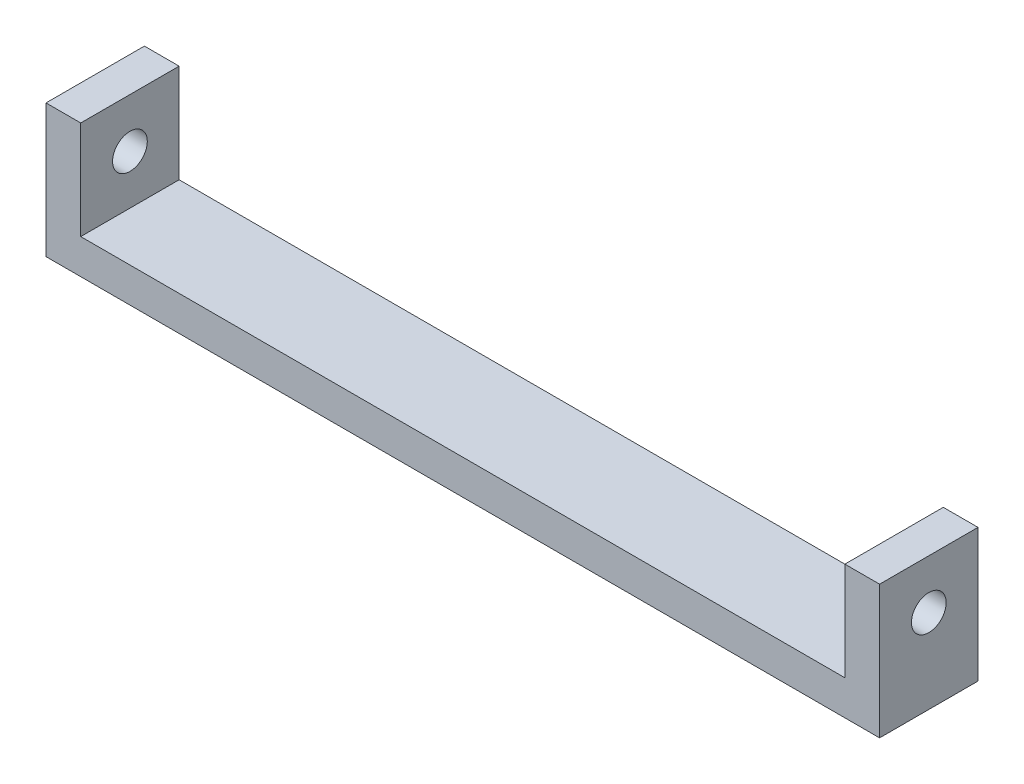
SolidWorks part; units mm, degrees
ref_plane "Front Plane" through (0, 0, 0) normal (0, 0, 1) x (1, 0, 0)
ref_plane "Top Plane" through (0, 0, 0) normal (0, 1, 0) x (1, 0, 0)
ref_plane "Right Plane" through (0, 0, 0) normal (1, 0, 0) x (0, 0, -1)
sketch "Sketch1" plane through (0, 0, 0) normal (1, 0, 0) x (0, 0, -1)
  line L0 (0, 0) -> (1.6017, 0) construction
  line L1 (1.5877, 2.75) -> (-1.5877, 2.75)
  line L2 (-1.5877, 2.75) -> (-3.1754, 0)
  line L3 (-3.1754, 0) -> (-1.5877, -2.75)
  line L4 (-1.5877, -2.75) -> (1.5877, -2.75)
  line L5 (1.5877, -2.75) -> (3.1754, 0)
  line L6 (3.1754, 0) -> (1.5877, 2.75)
  line L8 (-4.25, -4.25) -> (4.25, -4.25)
  line L9 (-4.25, -4.25) -> (-4.25, 4.25)
  line L10 (-4.25, 4.25) -> (4.25, 4.25)
  line L11 (4.25, -4.25) -> (4.25, 4.25)
  line L12 (-4.25, -4.25) -> (4.25, 4.25) construction
  line L13 (-4.25, 4.25) -> (4.25, -4.25) construction
  circle A0 centre (0, 0) radius 2.75 construction
  dimension "D1" = 5.5
  dimension "D2" = 8.5
  dimension "D3" = 8.5
extrude "Boss-Extrude1" add sketch "Sketch1" along normal blind 5
sketch "Sketch2" plane through (0, 0, 0) normal (-1, 0, 0) x (0, 0, 1)
  line L1 (-4.25, -4.25) -> (4.25, -4.25)
  line L2 (-4.25, -4.25) -> (-4.25, 4.25)
  line L3 (-4.25, 4.25) -> (4.25, 4.25)
  line L4 (4.25, -4.25) -> (4.25, 4.25)
  line L5 (-4.25, -4.25) -> (4.25, 4.25) construction
  line L6 (-4.25, 4.25) -> (4.25, -4.25) construction
  point P0 (0, 0)
extrude "Boss-Extrude2" add sketch "Sketch2" along normal blind 2
sketch "Sketch3" plane through (0, 0, 0) normal (1, 0, 0) x (0, 0, -1)
  circle A0 centre (0, 0) radius 1.5
  dimension "D1" = 3
extrude "Cut-Extrude1" cut sketch "Sketch3" against normal blind 2
sketch "Sketch4" plane through (0, -4.25, 0) normal (0, -1, 0) x (1, 0, 0)
  line L0 (5, -4.25) -> (-2, -4.25) construction
  line L1 (-2, 4.25) -> (78, 4.25)
  line L2 (-2, 4.25) -> (-2, -4.25)
  line L3 (-2, -4.25) -> (78, -4.25)
  line L4 (78, 4.25) -> (78, -4.25)
  dimension "D1" = 80
extrude "Boss-Extrude3" add sketch "Sketch4" along normal blind 3
sketch "Sketch5" plane through (0, -4.25, 0) normal (0, 1, 0) x (1, 0, 0)
  line L0 (78, -4.25) -> (5, -4.25) construction
  line L1 (78, 4.25) -> (71, 4.25)
  line L2 (78, 4.25) -> (78, -4.25)
  line L3 (78, -4.25) -> (71, -4.25)
  line L4 (71, 4.25) -> (71, -4.25)
  dimension "D1" = 7
extrude "Boss-Extrude4" add sketch "Sketch5" along normal up to surface (8.5 mm away) up to face at (1.5, 4.25, 0)
sketch "Sketch6" plane through (71, 0, 0) normal (-1, 0, 0) x (0, 0, 1)
  line L0 (-4.25, -4.25) -> (4.25, -4.25) construction
  line L1 (3.1754, 0) -> (1.5877, 2.75)
  line L2 (1.5877, 2.75) -> (-1.5877, 2.75)
  line L3 (-1.5877, 2.75) -> (-3.1754, 0)
  line L4 (-3.1754, 0) -> (-1.5877, -2.75)
  line L5 (-1.5877, -2.75) -> (1.5877, -2.75)
  line L6 (1.5877, -2.75) -> (3.1754, 0)
  circle A0 centre (0, 0) radius 2.75 construction
  dimension "D1" = 5.5
extrude "Cut-Extrude2" cut sketch "Sketch6" against normal blind 5
sketch "Sketch7" plane through (76, 0, 0) normal (-1, 0, 0) x (0, 0, 1)
  circle A0 centre (0, 0) radius 1.5
  dimension "D1" = 3
extrude "Cut-Extrude3" cut sketch "Sketch7" against normal blind 5
sketch "Sketch8" plane through (-2, 0, 0) normal (-1, 0, 0) x (0, 0, 1)
  line L0 (-1.5877, 2.75) -> (1.5877, 2.75) construction
  line L1 (1.5877, 2.75) -> (3.1754, 0) construction
  line L2 (3.1754, 0) -> (1.5877, -2.75) construction
  line L3 (1.5877, -2.75) -> (-1.5877, -2.75) construction
  line L4 (-1.5877, -2.75) -> (-3.1754, 0) construction
  line L5 (-3.1754, 0) -> (-1.5877, 2.75) construction
  line L6 (-1.5877, 2.75) -> (1.5877, 2.75)
  line L7 (1.5877, 2.75) -> (3.1754, 0)
  line L8 (3.1754, 0) -> (1.5877, -2.75)
  line L9 (1.5877, -2.75) -> (-1.5877, -2.75)
  line L10 (-1.5877, -2.75) -> (-3.1754, 0)
  line L11 (-3.1754, 0) -> (-1.5877, 2.75)
extrude "Cut-Extrude4" cut sketch "Sketch8" against normal blind 10
sketch "Sketch9" plane through (5, 0, 0) normal (1, 0, 0) x (0, 0, -1)
  line L1 (-4.25, 4.25) -> (4.25, 4.25)
  line L2 (-4.25, 4.25) -> (-4.25, -4.25)
  line L3 (-4.25, -4.25) -> (4.25, -4.25)
  line L4 (4.25, 4.25) -> (4.25, -4.25)
  circle A0 centre (0, 0) radius 1.5
  dimension "D1" = 3
extrude "Boss-Extrude5" add sketch "Sketch9" against normal blind 2
sketch "Sketch10" plane through (78, 0, 0) normal (1, 0, 0) x (0, 0, -1)
  line L0 (-3.1754, 0) -> (-1.5877, 2.75) construction
  line L1 (-1.5877, -2.75) -> (-3.1754, 0) construction
  line L2 (1.5877, -2.75) -> (-1.5877, -2.75) construction
  line L3 (3.1754, 0) -> (1.5877, -2.75) construction
  line L4 (1.5877, 2.75) -> (3.1754, 0) construction
  line L5 (-1.5877, 2.75) -> (1.5877, 2.75) construction
  line L6 (-3.1754, 0) -> (-1.5877, 2.75)
  line L7 (-1.5877, -2.75) -> (-3.1754, 0)
  line L8 (1.5877, -2.75) -> (-1.5877, -2.75)
  line L9 (3.1754, 0) -> (1.5877, -2.75)
  line L10 (1.5877, 2.75) -> (3.1754, 0)
  line L11 (-1.5877, 2.75) -> (1.5877, 2.75)
extrude "Cut-Extrude5" cut sketch "Sketch10" against normal blind 2
sketch "Sketch11" plane through (71, 0, 0) normal (-1, 0, 0) x (0, 0, 1)
  line L1 (-4.25, 4.25) -> (4.25, 4.25)
  line L2 (-4.25, 4.25) -> (-4.25, -4.25)
  line L3 (-4.25, -4.25) -> (4.25, -4.25)
  line L4 (4.25, 4.25) -> (4.25, -4.25)
  circle A0 centre (0, 0) radius 1.5
  dimension "D1" = 3
extrude "Boss-Extrude6" add sketch "Sketch11" against normal blind 2
sketch "Sketch12" plane through (3, 0, 0) normal (-1, 0, 0) x (0, 0, 1)
  line L0 (-3.1754, 0) -> (-1.5877, 2.75) construction
  line L1 (-1.5877, -2.75) -> (-3.1754, 0) construction
  line L2 (-1.5877, -2.75) -> (1.5877, -2.75) construction
  line L3 (1.5877, -2.75) -> (3.1754, 0) construction
  line L4 (3.1754, 0) -> (1.5877, 2.75) construction
  line L5 (-1.5877, 2.75) -> (1.5877, 2.75) construction
  line L6 (-3.1754, 0) -> (-1.5877, 2.75)
  line L7 (-1.5877, -2.75) -> (-3.1754, 0)
  line L8 (-1.5877, -2.75) -> (1.5877, -2.75)
  line L9 (1.5877, -2.75) -> (3.1754, 0)
  line L10 (3.1754, 0) -> (1.5877, 2.75)
  line L11 (-1.5877, 2.75) -> (1.5877, 2.75)
extrude "Boss-Extrude7" add sketch "Sketch12" along normal up to surface (5 mm away)
sketch "Sketch13" plane through (73, 0, 0) normal (1, 0, 0) x (0, 0, -1)
  line L0 (-1.5877, 2.75) -> (-3.1754, 0) construction
  line L1 (-3.1754, 0) -> (-1.5877, -2.75) construction
  line L2 (-1.5877, -2.75) -> (1.5877, -2.75) construction
  line L3 (1.5877, -2.75) -> (3.1754, 0) construction
  line L4 (3.1754, 0) -> (1.5877, 2.75) construction
  line L5 (1.5877, 2.75) -> (-1.5877, 2.75) construction
  line L6 (-1.5877, 2.75) -> (-3.1754, 0)
  line L7 (-3.1754, 0) -> (-1.5877, -2.75)
  line L8 (-1.5877, -2.75) -> (1.5877, -2.75)
  line L9 (1.5877, -2.75) -> (3.1754, 0)
  line L10 (3.1754, 0) -> (1.5877, 2.75)
  line L11 (1.5877, 2.75) -> (-1.5877, 2.75)
extrude "Boss-Extrude8" add sketch "Sketch13" along normal up to surface (5 mm away) up to face at (78, 0, 0)
sketch "Sketch14" plane through (-2, 0, 0) normal (-1, 0, 0) x (0, 0, 1)
  line L1 (-4.25, 4.25) -> (4.25, 4.25)
  line L2 (-4.25, 4.25) -> (-4.25, -7.25)
  line L3 (-4.25, -7.25) -> (4.25, -7.25)
  line L4 (4.25, 4.25) -> (4.25, -7.25)
extrude "Cut-Extrude6" cut sketch "Sketch14" against normal blind 4
sketch "Sketch15" plane through (78, 0, 0) normal (1, 0, 0) x (0, 0, -1)
  line L1 (-4.25, 4.25) -> (4.25, 4.25)
  line L2 (-4.25, 4.25) -> (-4.25, -7.25)
  line L3 (-4.25, -7.25) -> (4.25, -7.25)
  line L4 (4.25, 4.25) -> (4.25, -7.25)
extrude "Cut-Extrude7" cut sketch "Sketch15" against normal blind 4
sketch "Sketch16" plane through (5, 0, 0) normal (1, 0, 0) x (0, 0, -1)
  circle A0 centre (0, 0) radius 1.5
extrude "Cut-Extrude8" cut sketch "Sketch16" against normal blind 4
sketch "Sketch17" plane through (73, 0, 0) normal (-1, 0, 0) x (0, 0, 1)
  circle A0 centre (0, 0) radius 1.5
extrude "Cut-Extrude9" cut sketch "Sketch17" against normal blind 4
